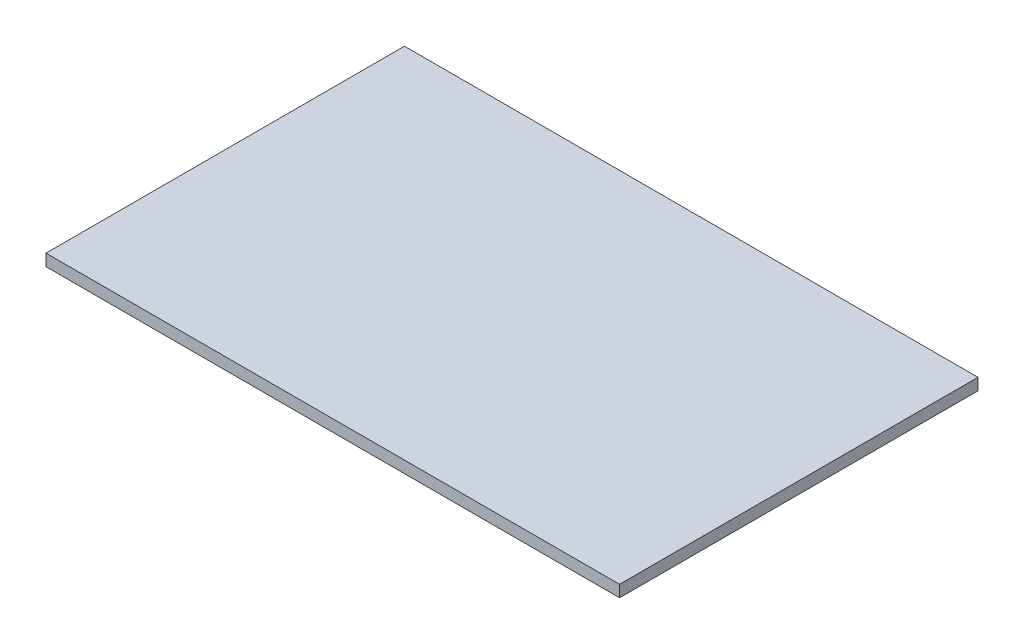
SolidWorks part; units mm, degrees
ref_plane "Спереди" through (0, 0, 0) normal (0, 0, 1) x (1, 0, 0)
ref_plane "Сверху" through (0, 0, 0) normal (0, 1, 0) x (1, 0, 0)
ref_plane "Справа" through (0, 0, 0) normal (1, 0, 0) x (0, 0, -1)
sketch "Эскиз1" plane through (0, 0, 0) normal (0, 1, 0) x (1, 0, 0)
  line L1 (440, -275) -> (-440, -275)
  line L2 (440, -275) -> (440, 275)
  line L3 (440, 275) -> (-440, 275)
  line L4 (-440, -275) -> (-440, 275)
  line L5 (440, -275) -> (-440, 275) construction
  line L6 (440, 275) -> (-440, -275) construction
  point P0 (0, 0)
  dimension "D1" = 880
  dimension "D2" = 550
extrude "Бобышка-Вытянуть1" add sketch "Эскиз1" along normal blind 18
